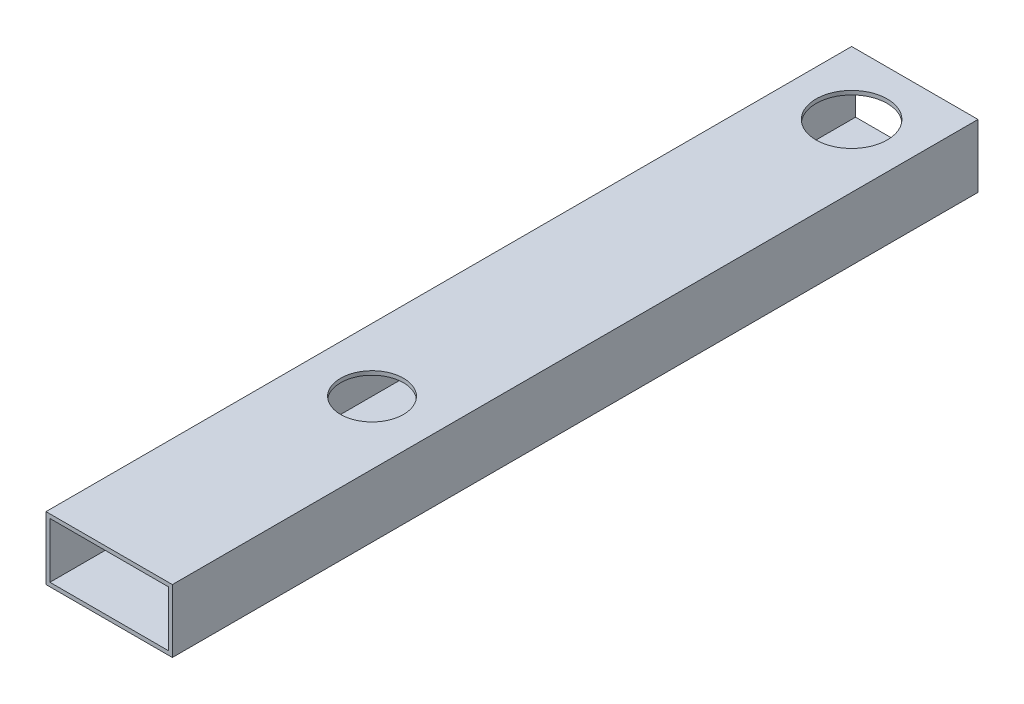
SolidWorks part; units mm, degrees
ref_plane "Front Plane" through (0, 0, 0) normal (0, 0, 1) x (1, 0, 0)
ref_plane "Top Plane" through (0, 0, 0) normal (0, 1, 0) x (1, 0, 0)
ref_plane "Right Plane" through (0, 0, 0) normal (1, 0, 0) x (0, 0, -1)
sketch "Sketch1" plane through (0, 0, 0) normal (0, 0, 1) x (1, 0, 0)
  line L1 (-7.2099, 5.457) -> (43.5901, 5.457)
  line L2 (-7.2099, 5.457) -> (-7.2099, -19.943)
  line L3 (-7.2099, -19.943) -> (43.5901, -19.943)
  line L4 (43.5901, 5.457) -> (43.5901, -19.943)
  line L5 (-5.6224, 3.8695) -> (42.0026, 3.8695)
  line L6 (-5.6224, 3.8695) -> (-5.6224, -18.3555)
  line L7 (-5.6224, -18.3555) -> (42.0026, -18.3555)
  line L8 (42.0026, 3.8695) -> (42.0026, -18.3555)
  dimension "D1" = 1.5875
  dimension "D2" = 1.5875
  dimension "D3" = 1.5875
  dimension "D4" = 1.5875
  dimension "D5" = 50.8
  dimension "D6" = 25.4
extrude "Boss-Extrude1" add sketch "Sketch1" along normal blind 323.85
sketch "Sketch2" plane through (0, 5.457, 0) normal (0, 1, 0) x (1, 0, 0)
  line L0 (43.5901, 0) -> (-7.2099, 0) construction
  line L1 (-7.2099, -323.85) -> (-7.2099, 0) construction
  circle A0 centre (18.1901, -25.4) radius 14.3056
  point P4 (18.1901, 0)
  dimension "D1" = 25.4
  dimension "D2" = 25.4
extrude "Cut-Extrude1" cut sketch "Sketch2" against normal through all
sketch "Sketch4" plane through (0, 5.457, 0) normal (0, 1, 0) x (1, 0, 0)
  line L0 (43.5901, -323.85) -> (-7.2099, -323.85) construction
  line L1 (-7.2099, -323.85) -> (-7.2099, 0) construction
  circle A1 centre (18.1901, -218.186) radius 12.6379
  dimension "D1" = 105.664
  dimension "D2" = 25.4
extrude "Cut-Extrude3" cut sketch "Sketch4" against normal through all
